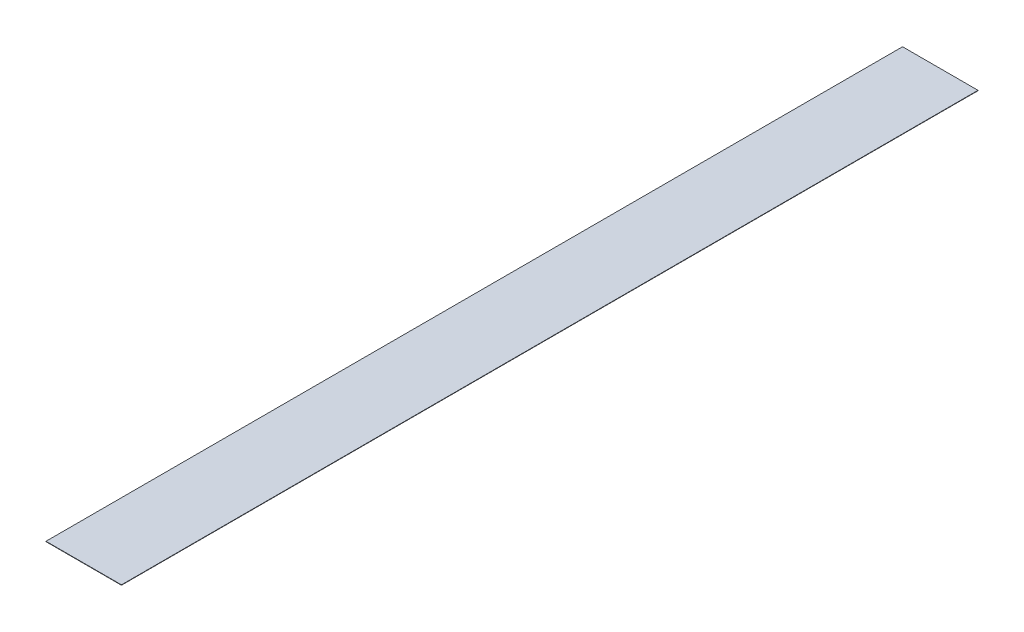
SolidWorks part; units mm, degrees
material "Mahogany"
ref_plane "Front Plane" through (0, 0, 0) normal (0, 0, 1) x (1, 0, 0)
ref_plane "Top Plane" through (0, 0, 0) normal (0, 1, 0) x (1, 0, 0)
ref_plane "Right Plane" through (0, 0, 0) normal (1, 0, 0) x (0, 0, -1)
sketch "Sketch1" plane through (0, 639.75, 0) normal (0, 1, 0) x (1, 0, 0)
  line L0 (-975, -2270) -> (975, -2270) construction
  line L1 (-975, 2270) -> (-575, 2270)
  line L2 (-975, 2270) -> (-975, -2270)
  line L3 (-975, -2270) -> (-575, -2270)
  line L4 (-575, 2270) -> (-575, -2270)
  line L7 (-575, -2220) -> (-575, 2220) construction
extrude "Boss-Extrude1" add sketch "Sketch1" along normal blind 2
